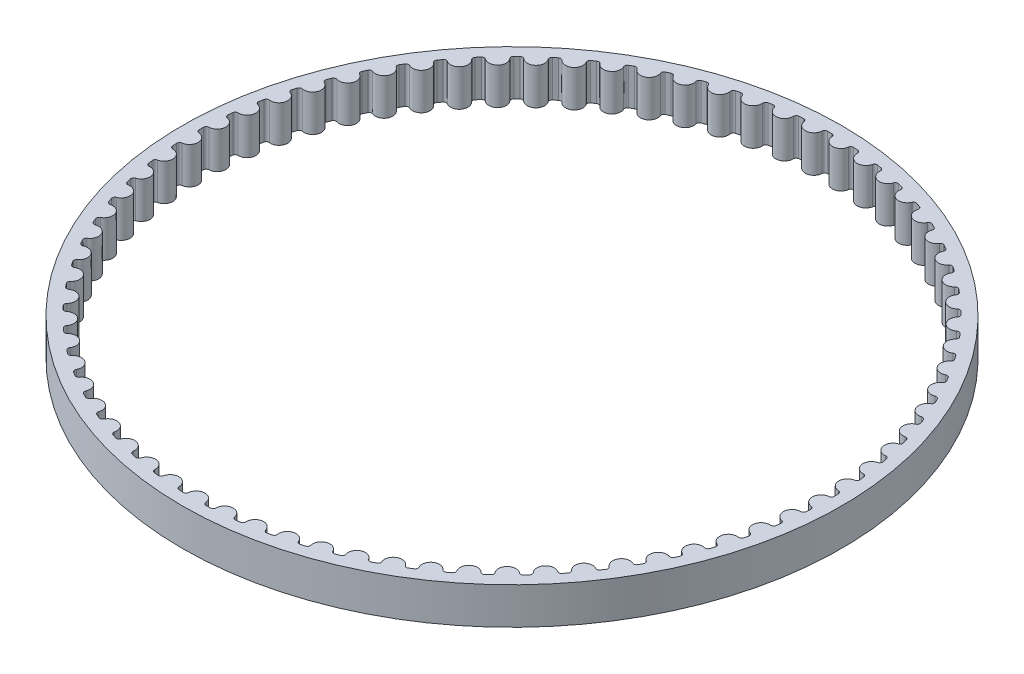
SolidWorks part; units mm, degrees
ref_plane "Front Plane" through (0, 0, 0) normal (0, 0, 1) x (1, 0, 0)
ref_plane "Top Plane" through (0, 0, 0) normal (0, 1, 0) x (1, 0, 0)
ref_plane "Right Plane" through (0, 0, 0) normal (1, 0, 0) x (0, 0, -1)
sketch "Sketch1" plane through (0, 0, 0) normal (0, 1, 0) x (1, 0, 0)
  circle A0 centre (0, 0) radius 35.7739
  arc B0 (-1.7188, -34.4311) -> (-1.2474, -34.4514) centre (0, 0) ccw
  arc B1 (-1.2474, -34.4514) -> (-0.9392, -34.184) centre (-1.2366, -34.1526) ccw
  arc B2 (0.9392, -34.184) -> (-0.9392, -34.184) centre (0, -34.2834) ccw
  arc B3 (0.9392, -34.184) -> (1.2474, -34.4514) centre (1.2366, -34.1526) ccw
  arc B4 (1.2474, -34.4514) -> (1.7188, -34.4311) centre (0, 0) ccw
  arc B5 (1.7188, -34.4311) -> (2.0029, -34.1382) centre (1.7039, -34.1324) ccw
  arc B6 (3.8744, -33.9767) -> (2.0029, -34.1382) centre (2.9472, -34.1565) ccw
  arc B7 (3.8744, -33.9767) -> (4.2044, -34.2166) centre (4.1679, -33.9198) ccw
  arc B8 (4.2044, -34.2166) -> (4.6723, -34.1558) centre (0, 0) ccw
  arc B9 (4.6723, -34.1558) -> (4.9301, -33.8397) centre (4.6318, -33.8596) ccw
  arc B10 (6.7809, -33.5179) -> (4.9301, -33.8397) centre (5.8725, -33.7767) ccw
  arc B11 (6.7809, -33.5179) -> (7.1302, -33.7285) centre (7.0684, -33.436) ccw
  arc B12 (7.1302, -33.7285) -> (7.5912, -33.6277) centre (0, 0) ccw
  arc B13 (7.5912, -33.6277) -> (7.8209, -33.2906) centre (7.5254, -33.3361) ccw
  arc B14 (9.6371, -32.8109) -> (7.8209, -33.2906) centre (8.7544, -33.1469) ccw
  arc B15 (9.6371, -32.8109) -> (10.0033, -32.9907) centre (9.9166, -32.7046) ccw
  arc B16 (10.0033, -32.9907) -> (10.4539, -32.8507) centre (0, 0) ccw
  arc B17 (10.4539, -32.8507) -> (10.6538, -32.495) centre (10.3633, -32.5658) ccw
  arc B18 (12.422, -31.861) -> (10.6538, -32.495) centre (11.5714, -32.2716) ccw
  arc B19 (12.422, -31.861) -> (12.8023, -32.0086) centre (12.6913, -31.731) ccw
  arc B20 (12.8023, -32.0086) -> (13.2392, -31.8304) centre (0, 0) ccw
  arc B21 (13.2392, -31.8304) -> (13.4078, -31.4589) centre (13.1244, -31.5543) ccw
  arc B22 (15.115, -30.6752) -> (13.4078, -31.4589) centre (14.3028, -31.1574) ccw
  arc B23 (15.115, -30.6752) -> (15.5065, -30.7896) centre (15.3721, -30.5225) ccw
  arc B24 (15.5065, -30.7896) -> (15.9265, -30.5745) centre (0, 0) ccw
  arc B25 (15.9265, -30.5745) -> (16.0625, -30.1898) centre (15.7884, -30.3093) ccw
  arc B26 (17.696, -29.2623) -> (16.0625, -30.1898) centre (16.9283, -29.8125) ccw
  arc B27 (17.696, -29.2623) -> (18.096, -29.3426) centre (17.939, -29.0881) ccw
  arc B28 (18.096, -29.3426) -> (18.4959, -29.0922) centre (0, 0) ccw
  arc B29 (18.4959, -29.0922) -> (18.5983, -28.6973) centre (18.3355, -28.8398) ccw
  arc B30 (20.146, -27.6327) -> (18.5983, -28.6973) centre (19.4285, -28.2469) ccw
  arc B31 (20.146, -27.6327) -> (20.5514, -27.6784) centre (20.3732, -27.4383) ccw
  arc B32 (20.5514, -27.6784) -> (20.9283, -27.3945) centre (0, 0) ccw
  arc B33 (20.9283, -27.3945) -> (20.9964, -26.9922) centre (20.7468, -27.1569) ccw
  arc B34 (22.4469, -25.7986) -> (20.9964, -26.9922) centre (21.7848, -26.4722) ccw
  arc B35 (22.4469, -25.7986) -> (22.8547, -25.8092) centre (22.6565, -25.5854) ccw
  arc B36 (22.8547, -25.8092) -> (23.2058, -25.494) centre (0, 0) ccw
  arc B37 (23.2058, -25.494) -> (23.239, -25.0874) centre (23.0045, -25.2729) ccw
  arc B38 (24.5816, -23.7734) -> (23.239, -25.0874) centre (23.9798, -24.5015) ccw
  arc B39 (24.5816, -23.7734) -> (24.9888, -23.749) centre (24.772, -23.543) ccw
  arc B40 (24.9888, -23.749) -> (25.3115, -23.4047) centre (0, 0) ccw
  arc B41 (25.3115, -23.4047) -> (25.3097, -22.9968) centre (25.092, -23.2017) ccw
  arc B42 (26.5342, -21.5723) -> (25.3097, -22.9968) centre (25.9973, -22.3493) ccw
  arc B43 (26.5342, -21.5723) -> (26.9378, -21.5129) centre (26.7042, -21.3263) ccw
  arc B44 (26.9378, -21.5129) -> (27.2298, -21.1422) centre (0, 0) ccw
  arc B45 (27.2298, -21.1422) -> (27.1929, -20.7359) centre (26.9936, -20.9588) ccw
  arc B46 (28.2905, -19.2114) -> (27.1929, -20.7359) centre (27.8223, -20.0317) ccw
  arc B47 (28.2905, -19.2114) -> (28.6875, -19.1175) centre (28.4387, -18.9517) ccw
  arc B48 (28.6875, -19.1175) -> (28.9464, -18.7231) centre (0, 0) ccw
  arc B49 (28.9464, -18.7231) -> (28.8748, -18.3215) centre (28.6954, -18.5607) ccw
  arc B50 (29.8372, -16.7083) -> (28.8748, -18.3215) centre (29.4414, -17.5659) ccw
  arc B51 (29.8372, -16.7083) -> (30.2247, -16.5807) centre (29.9626, -16.4369) ccw
  arc B52 (30.2247, -16.5807) -> (30.4488, -16.1654) centre (0, 0) ccw
  arc B53 (30.4488, -16.1654) -> (30.3429, -15.7715) centre (30.1847, -16.0252) ccw
  arc B54 (31.1631, -14.0815) -> (30.3429, -15.7715) centre (30.8424, -14.9699) ccw
  arc B55 (31.1631, -14.0815) -> (31.5382, -13.921) centre (31.2646, -13.8003) ccw
  arc B56 (31.5382, -13.921) -> (31.7258, -13.4881) centre (0, 0) ccw
  arc B57 (31.7258, -13.4881) -> (31.5863, -13.1047) centre (31.4506, -13.3711) ccw
  arc B58 (32.2583, -11.3505) -> (31.5863, -13.1047) centre (32.0151, -12.2631) ccw
  arc B59 (32.2583, -11.3505) -> (32.6182, -11.1583) centre (32.3352, -11.0615) ccw
  arc B60 (32.6182, -11.1583) -> (32.7678, -10.7108) centre (0, 0) ccw
  arc B61 (32.7678, -10.7108) -> (32.596, -10.3408) centre (32.4836, -10.6179) ccw
  arc B62 (33.1146, -8.5354) -> (32.596, -10.3408) centre (32.9508, -9.4656) ccw
  arc B63 (33.1146, -8.5354) -> (33.4566, -8.313) centre (33.1665, -8.2409) ccw
  arc B64 (33.4566, -8.313) -> (33.5673, -7.8543) centre (0, 0) ccw
  arc B65 (33.5673, -7.8543) -> (33.3642, -7.5005) centre (33.2761, -7.7862) ccw
  arc B66 (33.7258, -5.6571) -> (33.3642, -7.5005) centre (33.6426, -6.5979) ccw
  arc B67 (33.7258, -5.6571) -> (34.0474, -5.4061) centre (33.7521, -5.3592) ccw
  arc B68 (34.0474, -5.4061) -> (34.1182, -4.9396) centre (0, 0) ccw
  arc B69 (34.1182, -4.9396) -> (33.8855, -4.6045) centre (33.8223, -4.8968) ccw
  arc B70 (34.0872, -2.7369) -> (33.8855, -4.6045) centre (34.0852, -3.6814) ccw
  arc B71 (34.0872, -2.7369) -> (34.3861, -2.4592) centre (34.0879, -2.4379) ccw
  arc B72 (34.3861, -2.4592) -> (34.4165, -1.9884) centre (0, 0) ccw
  arc B73 (34.4165, -1.9884) -> (34.1559, -1.6745) centre (34.118, -1.9711) ccw
  arc B74 (34.1963, 0.2035) -> (34.1559, -1.6745) centre (34.2755, -0.7376) ccw
  arc B75 (34.1963, 0.2035) -> (34.4702, 0.5059) centre (34.1713, 0.5015) ccw
  arc B76 (34.4702, 0.5059) -> (34.4601, 0.9776) centre (0, 0) ccw
  arc B77 (34.4601, 0.9776) -> (34.1734, 1.2679) centre (34.1612, 0.9691) ccw
  arc B78 (34.0522, 3.1424) -> (34.1734, 1.2679) centre (34.212, 2.2116) ccw
  arc B79 (34.0522, 3.1424) -> (34.2991, 3.4672) centre (34.0016, 3.4371) ccw
  arc B80 (34.2991, 3.4672) -> (34.2485, 3.9363) centre (0, 0) ccw
  arc B81 (34.2485, 3.9363) -> (33.9379, 4.2009) centre (33.9514, 3.9022) ccw
  arc B82 (33.656, 6.0581) -> (33.9379, 4.2009) centre (33.8953, 5.1444) ccw
  arc B83 (33.656, 6.0581) -> (33.8741, 6.4029) centre (33.5803, 6.3474) ccw
  arc B84 (33.8741, 6.4029) -> (33.7833, 6.8659) centre (0, 0) ccw
  arc B85 (33.7833, 6.8659) -> (33.4512, 7.1028) centre (33.4903, 6.8064) ccw
  arc B86 (33.0107, 8.9289) -> (33.4512, 7.1028) centre (33.3275, 8.0392) ccw
  arc B87 (33.0107, 8.9289) -> (33.1983, 9.2912) centre (32.9103, 9.2106) ccw
  arc B88 (33.1983, 9.2912) -> (33.068, 9.7447) centre (0, 0) ccw
  arc B89 (33.068, 9.7447) -> (32.7167, 9.9521) centre (32.7812, 9.6602) ccw
  arc B90 (32.1209, 11.7336) -> (32.7167, 9.9521) centre (32.5131, 10.8744) ccw
  arc B91 (32.1209, 11.7336) -> (32.2767, 12.1107) centre (31.9967, 12.0056) ccw
  arc B92 (32.2767, 12.1107) -> (32.1079, 12.5513) centre (0, 0) ccw
  arc B93 (32.1079, 12.5513) -> (31.7401, 12.7278) centre (31.8294, 12.4424) ccw
  arc B94 (30.9933, 14.4514) -> (31.7401, 12.7278) centre (31.4579, 13.6291) ccw
  arc B95 (30.9933, 14.4514) -> (31.1161, 14.8405) centre (30.8462, 14.7118) ccw
  arc B96 (31.1161, 14.8405) -> (30.9101, 15.265) centre (0, 0) ccw
  arc B97 (30.9101, 15.265) -> (30.5285, 15.4092) centre (30.642, 15.1326) ccw
  arc B98 (29.6363, 17.0623) -> (30.5285, 15.4092) centre (30.1698, 16.283) ccw
  arc B99 (29.6363, 17.0623) -> (29.7252, 17.4604) centre (29.4673, 17.309) ccw
  arc B100 (29.7252, 17.4604) -> (29.4834, 17.8656) centre (0, 0) ccw
  arc B101 (29.4834, 17.8656) -> (29.0908, 17.9765) centre (29.2277, 17.7107) ccw
  arc B102 (28.0598, 19.5468) -> (29.0908, 17.9765) centre (28.6584, 18.8162) ccw
  arc B103 (28.0598, 19.5468) -> (28.1141, 19.9511) centre (27.8703, 19.7781) ccw
  arc B104 (28.1141, 19.9511) -> (27.8384, 20.334) centre (0, 0) ccw
  arc B105 (27.8384, 20.334) -> (27.4378, 20.4108) centre (27.597, 20.1577) ccw
  arc B106 (26.2756, 21.8866) -> (27.4378, 20.4108) centre (26.9348, 21.2102) ccw
  arc B107 (26.2756, 21.8866) -> (26.295, 22.2941) centre (26.0669, 22.1007) ccw
  arc B108 (26.295, 22.2941) -> (25.9874, 22.6519) centre (0, 0) ccw
  arc B109 (25.9874, 22.6519) -> (25.5816, 22.6939) centre (25.762, 22.4554) ccw
  arc B110 (24.2968, 24.0644) -> (25.5816, 22.6939) centre (25.0117, 23.4471) ccw
  arc B111 (24.2968, 24.0644) -> (24.2811, 24.472) centre (24.0705, 24.2598) ccw
  arc B112 (24.2811, 24.472) -> (23.9439, 24.802) centre (0, 0) ccw
  arc B113 (23.9439, 24.802) -> (23.536, 24.809) centre (23.7362, 24.5869) ccw
  arc B114 (22.1382, 26.0639) -> (23.536, 24.809) centre (22.9035, 25.5104) ccw
  arc B115 (22.1382, 26.0639) -> (22.0875, 26.4687) centre (21.8959, 26.2392) ccw
  arc B116 (22.0875, 26.4687) -> (21.7232, 26.7686) centre (0, 0) ccw
  arc B117 (21.7232, 26.7686) -> (21.3162, 26.7404) centre (21.5348, 26.5364) ccw
  arc B118 (19.8157, 27.8706) -> (21.3162, 26.7404) centre (20.6257, 27.3849) ccw
  arc B119 (19.8157, 27.8706) -> (19.7304, 28.2695) centre (19.5592, 28.0243) ccw
  arc B120 (19.7304, 28.2695) -> (19.3416, 28.5369) centre (0, 0) ccw
  arc B121 (19.3416, 28.5369) -> (18.9385, 28.4739) centre (19.1738, 28.2894) ccw
  arc B122 (17.3464, 29.4708) -> (18.9385, 28.4739) centre (18.1952, 29.0566) ccw
  arc B123 (17.3464, 29.4708) -> (17.2271, 29.861) centre (17.0777, 29.602) ccw
  arc B124 (17.2271, 29.861) -> (16.8168, 30.094) centre (0, 0) ccw
  arc B125 (16.8168, 30.094) -> (16.4207, 29.9965) centre (16.671, 29.8329) ccw
  arc B126 (14.7488, 30.8529) -> (16.4207, 29.9965) centre (15.63, 30.5132) ccw
  arc B127 (14.7488, 30.8529) -> (14.5964, 31.2314) centre (14.4698, 30.9605) ccw
  arc B128 (14.5964, 31.2314) -> (14.1676, 31.4282) centre (0, 0) ccw
  arc B129 (14.1676, 31.4282) -> (13.7812, 31.2971) centre (14.0447, 31.1556) ccw
  arc B130 (12.0419, 32.0066) -> (13.7812, 31.2971) centre (12.9491, 31.7439) ccw
  arc B131 (12.0419, 32.0066) -> (11.8576, 32.3705) centre (11.7547, 32.0898) ccw
  arc B132 (11.8576, 32.3705) -> (11.4134, 32.5298) centre (0, 0) ccw
  arc B133 (11.4134, 32.5298) -> (11.0398, 32.3659) centre (11.3144, 32.2476) ccw
  arc B134 (9.2459, 32.9233) -> (11.0398, 32.3659) centre (10.1723, 32.7395) ccw
  arc B135 (9.2459, 32.9233) -> (9.0309, 33.27) centre (8.9526, 32.9815) ccw
  arc B136 (9.0309, 33.27) -> (8.5747, 33.3905) centre (0, 0) ccw
  arc B137 (8.5747, 33.3905) -> (8.2166, 33.1951) centre (8.5004, 33.1009) ccw
  arc B138 (6.3814, 33.5962) -> (8.2166, 33.1951) centre (7.3202, 33.4928) ccw
  arc B139 (6.3814, 33.5962) -> (6.1374, 33.9232) centre (6.0842, 33.629) ccw
  arc B140 (6.1374, 33.9232) -> (5.6726, 34.004) centre (0, 0) ccw
  arc B141 (5.6726, 34.004) -> (5.3326, 33.7786) centre (5.6234, 33.7091) ccw
  arc B142 (3.4697, 34.0204) -> (5.3326, 33.7786) centre (4.4139, 33.9981) ccw
  arc B143 (3.4697, 34.0204) -> (3.1985, 34.3252) centre (3.1708, 34.0275) ccw
  arc B144 (3.1985, 34.3252) -> (2.7284, 34.3658) centre (0, 0) ccw
  arc B145 (2.7284, 34.3658) -> (2.409, 34.112) centre (2.7048, 34.0677) ccw
  arc B146 (0.5323, 34.1928) -> (2.409, 34.112) centre (1.4749, 34.2517) ccw
  arc B147 (0.5323, 34.1928) -> (0.2359, 34.4731) centre (0.2339, 34.1741) ccw
  arc B148 (0.2359, 34.4731) -> (-0.2359, 34.4731) centre (0, 0) ccw
  arc B149 (-0.2359, 34.4731) -> (-0.5323, 34.1928) centre (-0.2339, 34.1741) ccw
  arc B150 (-2.409, 34.112) -> (-0.5323, 34.1928) centre (-1.4749, 34.2517) ccw
  arc B151 (-2.409, 34.112) -> (-2.7284, 34.3658) centre (-2.7048, 34.0677) ccw
  arc B152 (-2.7284, 34.3658) -> (-3.1985, 34.3252) centre (0, 0) ccw
  arc B153 (-3.1985, 34.3252) -> (-3.4697, 34.0204) centre (-3.1708, 34.0275) ccw
  arc B154 (-5.3326, 33.7786) -> (-3.4697, 34.0204) centre (-4.4139, 33.9981) ccw
  arc B155 (-5.3326, 33.7786) -> (-5.6726, 34.004) centre (-5.6234, 33.7091) ccw
  arc B156 (-5.6726, 34.004) -> (-6.1374, 33.9232) centre (0, 0) ccw
  arc B157 (-6.1374, 33.9232) -> (-6.3814, 33.5962) centre (-6.0842, 33.629) ccw
  arc B158 (-8.2166, 33.1951) -> (-6.3814, 33.5962) centre (-7.3202, 33.4928) ccw
  arc B159 (-8.2166, 33.1951) -> (-8.5747, 33.3905) centre (-8.5004, 33.1009) ccw
  arc B160 (-8.5747, 33.3905) -> (-9.0309, 33.27) centre (0, 0) ccw
  arc B161 (-9.0309, 33.27) -> (-9.2459, 32.9233) centre (-8.9526, 32.9815) ccw
  arc B162 (-11.0398, 32.3659) -> (-9.2459, 32.9233) centre (-10.1723, 32.7395) ccw
  arc B163 (-11.0398, 32.3659) -> (-11.4134, 32.5298) centre (-11.3144, 32.2476) ccw
  arc B164 (-11.4134, 32.5298) -> (-11.8576, 32.3705) centre (0, 0) ccw
  arc B165 (-11.8576, 32.3705) -> (-12.0419, 32.0066) centre (-11.7547, 32.0898) ccw
  arc B166 (-13.7812, 31.2971) -> (-12.0419, 32.0066) centre (-12.9491, 31.7439) ccw
  arc B167 (-13.7812, 31.2971) -> (-14.1676, 31.4282) centre (-14.0447, 31.1556) ccw
  arc B168 (-14.1676, 31.4282) -> (-14.5964, 31.2314) centre (0, 0) ccw
  arc B169 (-14.5964, 31.2314) -> (-14.7488, 30.8529) centre (-14.4698, 30.9605) ccw
  arc B170 (-16.4207, 29.9965) -> (-14.7488, 30.8529) centre (-15.63, 30.5132) ccw
  arc B171 (-16.4207, 29.9965) -> (-16.8168, 30.094) centre (-16.671, 29.8329) ccw
  arc B172 (-16.8168, 30.094) -> (-17.2271, 29.861) centre (0, 0) ccw
  arc B173 (-17.2271, 29.861) -> (-17.3464, 29.4708) centre (-17.0777, 29.602) ccw
  arc B174 (-18.9385, 28.4739) -> (-17.3464, 29.4708) centre (-18.1952, 29.0566) ccw
  arc B175 (-18.9385, 28.4739) -> (-19.3416, 28.5369) centre (-19.1738, 28.2894) ccw
  arc B176 (-19.3416, 28.5369) -> (-19.7304, 28.2695) centre (0, 0) ccw
  arc B177 (-19.7304, 28.2695) -> (-19.8157, 27.8706) centre (-19.5592, 28.0243) ccw
  arc B178 (-21.3162, 26.7404) -> (-19.8157, 27.8706) centre (-20.6257, 27.3849) ccw
  arc B179 (-21.3162, 26.7404) -> (-21.7232, 26.7686) centre (-21.5348, 26.5364) ccw
  arc B180 (-21.7232, 26.7686) -> (-22.0875, 26.4687) centre (0, 0) ccw
  arc B181 (-22.0875, 26.4687) -> (-22.1382, 26.0639) centre (-21.8959, 26.2392) ccw
  arc B182 (-23.536, 24.809) -> (-22.1382, 26.0639) centre (-22.9035, 25.5104) ccw
  arc B183 (-23.536, 24.809) -> (-23.9439, 24.802) centre (-23.7362, 24.5869) ccw
  arc B184 (-23.9439, 24.802) -> (-24.2811, 24.472) centre (0, 0) ccw
  arc B185 (-24.2811, 24.472) -> (-24.2968, 24.0644) centre (-24.0705, 24.2598) ccw
  arc B186 (-25.5816, 22.6939) -> (-24.2968, 24.0644) centre (-25.0117, 23.4471) ccw
  arc B187 (-25.5816, 22.6939) -> (-25.9874, 22.6519) centre (-25.762, 22.4554) ccw
  arc B188 (-25.9874, 22.6519) -> (-26.295, 22.2941) centre (0, 0) ccw
  arc B189 (-26.295, 22.2941) -> (-26.2756, 21.8866) centre (-26.0669, 22.1007) ccw
  arc B190 (-27.4378, 20.4108) -> (-26.2756, 21.8866) centre (-26.9348, 21.2102) ccw
  arc B191 (-27.4378, 20.4108) -> (-27.8384, 20.334) centre (-27.597, 20.1577) ccw
  arc B192 (-27.8384, 20.334) -> (-28.1141, 19.9511) centre (0, 0) ccw
  arc B193 (-28.1141, 19.9511) -> (-28.0598, 19.5468) centre (-27.8703, 19.7781) ccw
  arc B194 (-29.0908, 17.9765) -> (-28.0598, 19.5468) centre (-28.6584, 18.8162) ccw
  arc B195 (-29.0908, 17.9765) -> (-29.4834, 17.8656) centre (-29.2277, 17.7107) ccw
  arc B196 (-29.4834, 17.8656) -> (-29.7252, 17.4604) centre (0, 0) ccw
  arc B197 (-29.7252, 17.4604) -> (-29.6363, 17.0623) centre (-29.4673, 17.309) ccw
  arc B198 (-30.5285, 15.4092) -> (-29.6363, 17.0623) centre (-30.1698, 16.283) ccw
  arc B199 (-30.5285, 15.4092) -> (-30.9101, 15.265) centre (-30.642, 15.1326) ccw
  arc B200 (-30.9101, 15.265) -> (-31.1161, 14.8405) centre (0, 0) ccw
  arc B201 (-31.1161, 14.8405) -> (-30.9933, 14.4514) centre (-30.8462, 14.7118) ccw
  arc B202 (-31.7401, 12.7278) -> (-30.9933, 14.4514) centre (-31.4579, 13.6291) ccw
  arc B203 (-31.7401, 12.7278) -> (-32.1079, 12.5513) centre (-31.8294, 12.4424) ccw
  arc B204 (-32.1079, 12.5513) -> (-32.2767, 12.1107) centre (0, 0) ccw
  arc B205 (-32.2767, 12.1107) -> (-32.1209, 11.7336) centre (-31.9967, 12.0056) ccw
  arc B206 (-32.7167, 9.9521) -> (-32.1209, 11.7336) centre (-32.5131, 10.8744) ccw
  arc B207 (-32.7167, 9.9521) -> (-33.068, 9.7447) centre (-32.7812, 9.6602) ccw
  arc B208 (-33.068, 9.7447) -> (-33.1983, 9.2912) centre (0, 0) ccw
  arc B209 (-33.1983, 9.2912) -> (-33.0107, 8.9289) centre (-32.9103, 9.2106) ccw
  arc B210 (-33.4512, 7.1028) -> (-33.0107, 8.9289) centre (-33.3275, 8.0392) ccw
  arc B211 (-33.4512, 7.1028) -> (-33.7833, 6.8659) centre (-33.4903, 6.8064) ccw
  arc B212 (-33.7833, 6.8659) -> (-33.8741, 6.4029) centre (0, 0) ccw
  arc B213 (-33.8741, 6.4029) -> (-33.656, 6.0581) centre (-33.5803, 6.3474) ccw
  arc B214 (-33.9379, 4.2009) -> (-33.656, 6.0581) centre (-33.8953, 5.1444) ccw
  arc B215 (-33.9379, 4.2009) -> (-34.2485, 3.9363) centre (-33.9514, 3.9022) ccw
  arc B216 (-34.2485, 3.9363) -> (-34.2991, 3.4672) centre (0, 0) ccw
  arc B217 (-34.2991, 3.4672) -> (-34.0522, 3.1424) centre (-34.0016, 3.4371) ccw
  arc B218 (-34.1734, 1.2679) -> (-34.0522, 3.1424) centre (-34.212, 2.2116) ccw
  arc B219 (-34.1734, 1.2679) -> (-34.4601, 0.9776) centre (-34.1612, 0.9691) ccw
  arc B220 (-34.4601, 0.9776) -> (-34.4702, 0.5059) centre (0, 0) ccw
  arc B221 (-34.4702, 0.5059) -> (-34.1963, 0.2035) centre (-34.1713, 0.5015) ccw
  arc B222 (-34.1559, -1.6745) -> (-34.1963, 0.2035) centre (-34.2755, -0.7376) ccw
  arc B223 (-34.1559, -1.6745) -> (-34.4165, -1.9884) centre (-34.118, -1.9711) ccw
  arc B224 (-34.4165, -1.9884) -> (-34.3861, -2.4592) centre (0, 0) ccw
  arc B225 (-34.3861, -2.4592) -> (-34.0872, -2.7369) centre (-34.0879, -2.4379) ccw
  arc B226 (-33.8855, -4.6045) -> (-34.0872, -2.7369) centre (-34.0852, -3.6814) ccw
  arc B227 (-33.8855, -4.6045) -> (-34.1182, -4.9396) centre (-33.8223, -4.8968) ccw
  arc B228 (-34.1182, -4.9396) -> (-34.0474, -5.4061) centre (0, 0) ccw
  arc B229 (-34.0474, -5.4061) -> (-33.7258, -5.6571) centre (-33.7521, -5.3592) ccw
  arc B230 (-33.3642, -7.5005) -> (-33.7258, -5.6571) centre (-33.6426, -6.5979) ccw
  arc B231 (-33.3642, -7.5005) -> (-33.5673, -7.8543) centre (-33.2761, -7.7862) ccw
  arc B232 (-33.5673, -7.8543) -> (-33.4566, -8.313) centre (0, 0) ccw
  arc B233 (-33.4566, -8.313) -> (-33.1146, -8.5354) centre (-33.1665, -8.2409) ccw
  arc B234 (-32.596, -10.3408) -> (-33.1146, -8.5354) centre (-32.9508, -9.4656) ccw
  arc B235 (-32.596, -10.3408) -> (-32.7678, -10.7108) centre (-32.4836, -10.6179) ccw
  arc B236 (-32.7678, -10.7108) -> (-32.6182, -11.1583) centre (0, 0) ccw
  arc B237 (-32.6182, -11.1583) -> (-32.2583, -11.3505) centre (-32.3352, -11.0615) ccw
  arc B238 (-31.5863, -13.1047) -> (-32.2583, -11.3505) centre (-32.0151, -12.2631) ccw
  arc B239 (-31.5863, -13.1047) -> (-31.7258, -13.4881) centre (-31.4506, -13.3711) ccw
  arc B240 (-31.7258, -13.4881) -> (-31.5382, -13.921) centre (0, 0) ccw
  arc B241 (-31.5382, -13.921) -> (-31.1631, -14.0815) centre (-31.2646, -13.8003) ccw
  arc B242 (-30.3429, -15.7715) -> (-31.1631, -14.0815) centre (-30.8424, -14.9699) ccw
  arc B243 (-30.3429, -15.7715) -> (-30.4488, -16.1654) centre (-30.1847, -16.0252) ccw
  arc B244 (-30.4488, -16.1654) -> (-30.2247, -16.5807) centre (0, 0) ccw
  arc B245 (-30.2247, -16.5807) -> (-29.8372, -16.7083) centre (-29.9626, -16.4369) ccw
  arc B246 (-28.8748, -18.3215) -> (-29.8372, -16.7083) centre (-29.4414, -17.5659) ccw
  arc B247 (-28.8748, -18.3215) -> (-28.9464, -18.7231) centre (-28.6954, -18.5607) ccw
  arc B248 (-28.9464, -18.7231) -> (-28.6875, -19.1175) centre (0, 0) ccw
  arc B249 (-28.6875, -19.1175) -> (-28.2905, -19.2114) centre (-28.4387, -18.9517) ccw
  arc B250 (-27.1929, -20.7359) -> (-28.2905, -19.2114) centre (-27.8223, -20.0317) ccw
  arc B251 (-27.1929, -20.7359) -> (-27.2298, -21.1422) centre (-26.9936, -20.9588) ccw
  arc B252 (-27.2298, -21.1422) -> (-26.9378, -21.5129) centre (0, 0) ccw
  arc B253 (-26.9378, -21.5129) -> (-26.5342, -21.5723) centre (-26.7042, -21.3263) ccw
  arc B254 (-25.3097, -22.9968) -> (-26.5342, -21.5723) centre (-25.9973, -22.3493) ccw
  arc B255 (-25.3097, -22.9968) -> (-25.3115, -23.4047) centre (-25.092, -23.2017) ccw
  arc B256 (-25.3115, -23.4047) -> (-24.9888, -23.749) centre (0, 0) ccw
  arc B257 (-24.9888, -23.749) -> (-24.5816, -23.7734) centre (-24.772, -23.543) ccw
  arc B258 (-23.239, -25.0874) -> (-24.5816, -23.7734) centre (-23.9798, -24.5015) ccw
  arc B259 (-23.239, -25.0874) -> (-23.2058, -25.494) centre (-23.0045, -25.2729) ccw
  arc B260 (-23.2058, -25.494) -> (-22.8547, -25.8092) centre (0, 0) ccw
  arc B261 (-22.8547, -25.8092) -> (-22.4469, -25.7986) centre (-22.6565, -25.5854) ccw
  arc B262 (-20.9964, -26.9922) -> (-22.4469, -25.7986) centre (-21.7848, -26.4722) ccw
  arc B263 (-20.9964, -26.9922) -> (-20.9283, -27.3945) centre (-20.7468, -27.1569) ccw
  arc B264 (-20.9283, -27.3945) -> (-20.5514, -27.6784) centre (0, 0) ccw
  arc B265 (-20.5514, -27.6784) -> (-20.146, -27.6327) centre (-20.3732, -27.4383) ccw
  arc B266 (-18.5983, -28.6973) -> (-20.146, -27.6327) centre (-19.4285, -28.2469) ccw
  arc B267 (-18.5983, -28.6973) -> (-18.4959, -29.0922) centre (-18.3355, -28.8398) ccw
  arc B268 (-18.4959, -29.0922) -> (-18.096, -29.3426) centre (0, 0) ccw
  arc B269 (-18.096, -29.3426) -> (-17.696, -29.2623) centre (-17.939, -29.0881) ccw
  arc B270 (-16.0625, -30.1898) -> (-17.696, -29.2623) centre (-16.9283, -29.8125) ccw
  arc B271 (-16.0625, -30.1898) -> (-15.9265, -30.5745) centre (-15.7884, -30.3093) ccw
  arc B272 (-15.9265, -30.5745) -> (-15.5065, -30.7896) centre (0, 0) ccw
  arc B273 (-15.5065, -30.7896) -> (-15.115, -30.6752) centre (-15.3721, -30.5225) ccw
  arc B274 (-13.4078, -31.4589) -> (-15.115, -30.6752) centre (-14.3028, -31.1574) ccw
  arc B275 (-13.4078, -31.4589) -> (-13.2392, -31.8304) centre (-13.1244, -31.5543) ccw
  arc B276 (-13.2392, -31.8304) -> (-12.8023, -32.0086) centre (0, 0) ccw
  arc B277 (-12.8023, -32.0086) -> (-12.422, -31.861) centre (-12.6913, -31.731) ccw
  arc B278 (-10.6538, -32.495) -> (-12.422, -31.861) centre (-11.5714, -32.2716) ccw
  arc B279 (-10.6538, -32.495) -> (-10.4539, -32.8507) centre (-10.3633, -32.5658) ccw
  arc B280 (-10.4539, -32.8507) -> (-10.0033, -32.9907) centre (0, 0) ccw
  arc B281 (-10.0033, -32.9907) -> (-9.6371, -32.8109) centre (-9.9166, -32.7046) ccw
  arc B282 (-7.8209, -33.2906) -> (-9.6371, -32.8109) centre (-8.7544, -33.1469) ccw
  arc B283 (-7.8209, -33.2906) -> (-7.5912, -33.6277) centre (-7.5254, -33.3361) ccw
  arc B284 (-7.5912, -33.6277) -> (-7.1302, -33.7285) centre (0, 0) ccw
  arc B285 (-7.1302, -33.7285) -> (-6.7809, -33.5179) centre (-7.0684, -33.436) ccw
  arc B286 (-4.9301, -33.8397) -> (-6.7809, -33.5179) centre (-5.8725, -33.7767) ccw
  arc B287 (-4.9301, -33.8397) -> (-4.6723, -34.1558) centre (-4.6318, -33.8596) ccw
  arc B288 (-4.6723, -34.1558) -> (-4.2044, -34.2166) centre (0, 0) ccw
  arc B289 (-4.2044, -34.2166) -> (-3.8744, -33.9767) centre (-4.1679, -33.9198) ccw
  arc B290 (-2.0029, -34.1382) -> (-3.8744, -33.9767) centre (-2.9472, -34.1565) ccw
  arc B291 (-2.0029, -34.1382) -> (-1.7188, -34.4311) centre (-1.7039, -34.1324) ccw
  dimension "D1" = 1.3
sketch_block_instance "Block-73T GT2 Pulley-1"
sketch_block "Block-73T GT2 Pulley"
extrude "Boss-Extrude1" add sketch "Sketch1" along normal blind 4
